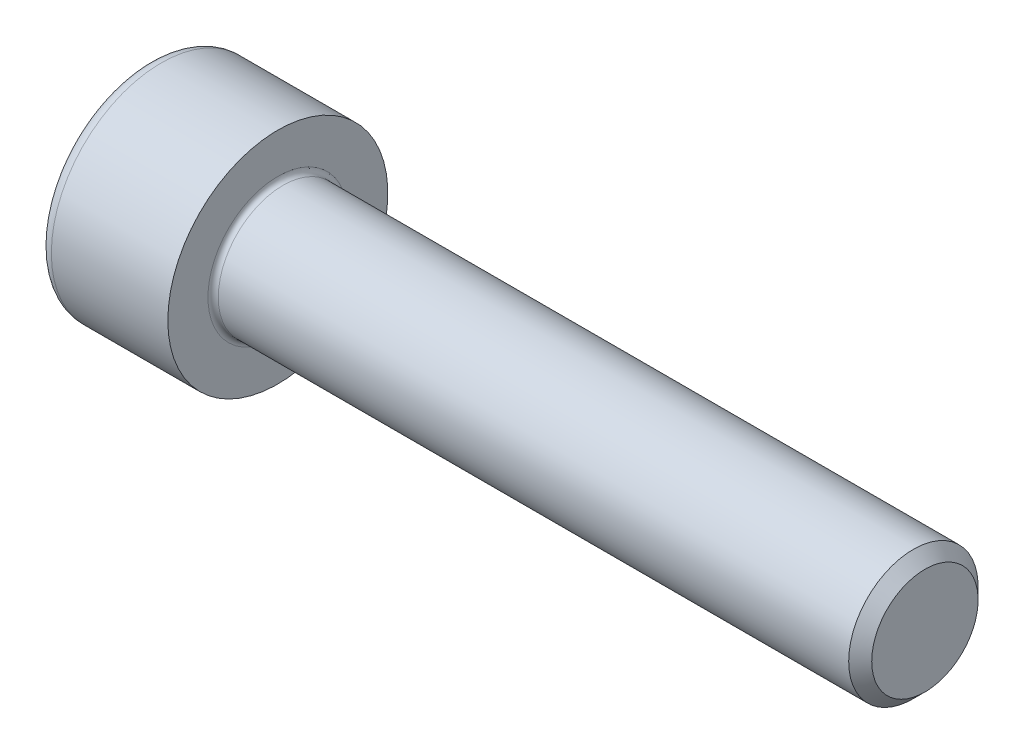
SolidWorks part; units mm, degrees
revolve "Base-Revolve" add sketch "BodySke"
sketch "BodySke" plane through (0, 0, 0) normal (0, 0, 1) x (1, 0, 0)
  line L0 (0, 0) -> (0, 4.25)
  line L1 (0, 4.25) -> (5, 4.25)
  line L2 (5, 4.25) -> (5, 2.5)
  line L3 (5, 2.5) -> (29.555, 2.5)
  line L4 (30, 2.055) -> (30, 0)
  line L5 (30, 0) -> (0, 0)
  line L6 (-31.75, 0) -> (127, 0) construction
  line L8 (30, 2.055) -> (29.555, 2.5)
  line L10 (30, -2.055) -> (29.555, -2.5) construction
  line L11 (5.8, 9.525) -> (5.8, 3.175) construction
  line L12 (8, 9.525) -> (8, 3.175) construction
  line L13 (5, 9.525) -> (5, 3.175) construction
  dimension "Head_ht" = 5
  dimension "Length" = 25
  dimension "Body_ch_ang" = 45
  dimension "Diameter" = 5
  dimension "Minor_dia" = 4.11
  dimension "Advance" = 0.8
  dimension "Thread_nom" = 22
  dimension "Thread_length" = 25
  dimension "Head_dia" = 8.5
cosmetic thread "ThreadCosmetic" [suppressed]
fillet "Fillet1" radius 0.2 1 edges at (5, 0, 2.5)
fillet "Fillet2" radius 0.5 1 edges at (0, 0, 4.25)
ref_plane "Plane1" through (0, 0, 0) normal (0, 0, 1) x (1, 0, 0)
ref_plane "Plane2" through (0, 0, 0) normal (0, 1, 0) x (1, 0, 0)
ref_plane "Plane3" through (0, 0, 0) normal (1, 0, 0) x (0, 0, -1)
sketch "Sketch2" plane through (0, 0, 0) normal (0, 0, 1) x (1, 0, 0)
  line L0 (0, 2.01) -> (2.5, 2.01)
  line L1 (2.5, 2.01) -> (3.6605, 0)
  line L2 (-31.75, 0) -> (127, 0) construction
  line L3 (3.6605, 0) -> (0, 0)
  line L4 (0, 0) -> (0, 2.01)
  line L6 (0, 0) -> (47.625, 0) construction
  dimension "D1" = 2.01
  dimension "D2" = 60
  dimension "Depth" = 2.5
revolve "Hex-PreBroach" cut sketch "Sketch2" angle 360 about L6
sketch "Sketch3" plane through (0, 0, 0) normal (-1, 0, 0) x (0, 0.5, 0.866)
  line L0 (1.1605, 2.01) -> (-1.1605, 2.01)
  line L1 (-1.1605, 2.01) -> (-2.3209, 0)
  line L2 (1.1605, 2.01) -> (2.3209, 0)
  line L3 (1.1605, -2.01) -> (2.3209, 0)
  line L4 (1.1605, -2.01) -> (-1.1605, -2.01)
  line L5 (-1.1605, -2.01) -> (-2.3209, 0)
  dimension "D1" = 2.01
  dimension "D2" = 2.01
  dimension "Hex_size" = 4.02
extrude "Hex" cut sketch "Sketch3" against normal blind 2.5
sketch "ThdSchSke" plane through (0, 0, 0) normal (0, 0, 1) x (1, 0, 0)
  line L0 (8, -2.055) -> (7.6884, -2.5)
  line L1 (8, -2.055) -> (8.3116, -2.5)
  line L2 (8.3116, -2.5) -> (8.3116, -3.125)
  line L3 (-3.175, 0) -> (5.1513, 0) construction
  line L4 (0, 3.75) -> (0, -3.75) construction
  line L5 (8.3116, -3.125) -> (7.6884, -3.125)
  line L6 (7.6884, -3.125) -> (7.6884, -2.5)
  dimension "Thread_minor" = 4.11
  dimension "Diameter" = 5
  dimension "Start" = 8
revolve "ThreadSchematic" [suppressed] cut sketch "ThdSchSke" angle 360 about L3
pattern_linear "ThdSchPat" [suppressed]
equation "\"D2@Sketch3\" = \"Hex_size@Sketch3\" / 2"
equation "\"D1@Sketch3\" = \"Hex_size@Sketch3\" / 2"
equation "\"D1@Sketch2\" = \"Hex_size@Sketch3\" / 2"
equation "\"Thread_minor@ThreadCosmetic\"  =  \"Minor_dia@BodySke\""
equation "\"Depth@Sketch2\" =  \"Key_eng@Hex\""
equation "\"Thread_length@ThreadCosmetic\" = ((sgn( (\"Length@BodySke\" - \"Advance@BodySke\" * 3.0) - \"Thread_nom@BodySke\" )-1)*( (\"Length@BodySke\" - \"Advance@BodySke\" * 3.0) - \"Thread_nom@BodySke\" ))/-2+ \"Thread_nom@BodySke\""
equation "\"Thread_minor@ThdSchSke\" = \"Minor_dia@BodySke\""
equation "\"Diameter@ThdSchSke\" = \"Diameter@BodySke\""
equation "\"Overcut@ThdSchSke\" = \"Diameter@BodySke\" * 1.25"
equation "\"Start@ThdSchSke\" = \"Head_ht@BodySke\" + \"Length@BodySke\" - \"Thread_length@ThreadCosmetic\"  '---Non-countersunk---"
equation "\"Num_threads@ThdSchPat\" = int( \"Thread_length@ThreadCosmetic\" / \"Advance@BodySke\" + 0.999 )  + 1"
equation "\"Advance@ThdSchPat\" = \"Thread_length@ThreadCosmetic\" /  (\"Num_threads@ThdSchPat\" - 1) 'relax it"
equation "\"Num_threads@ThdSchPat\" = \"Num_threads@ThdSchPat\" - sgn( \"Num_threads@ThdSchPat\" - 1) '---chamfered tips only---"
